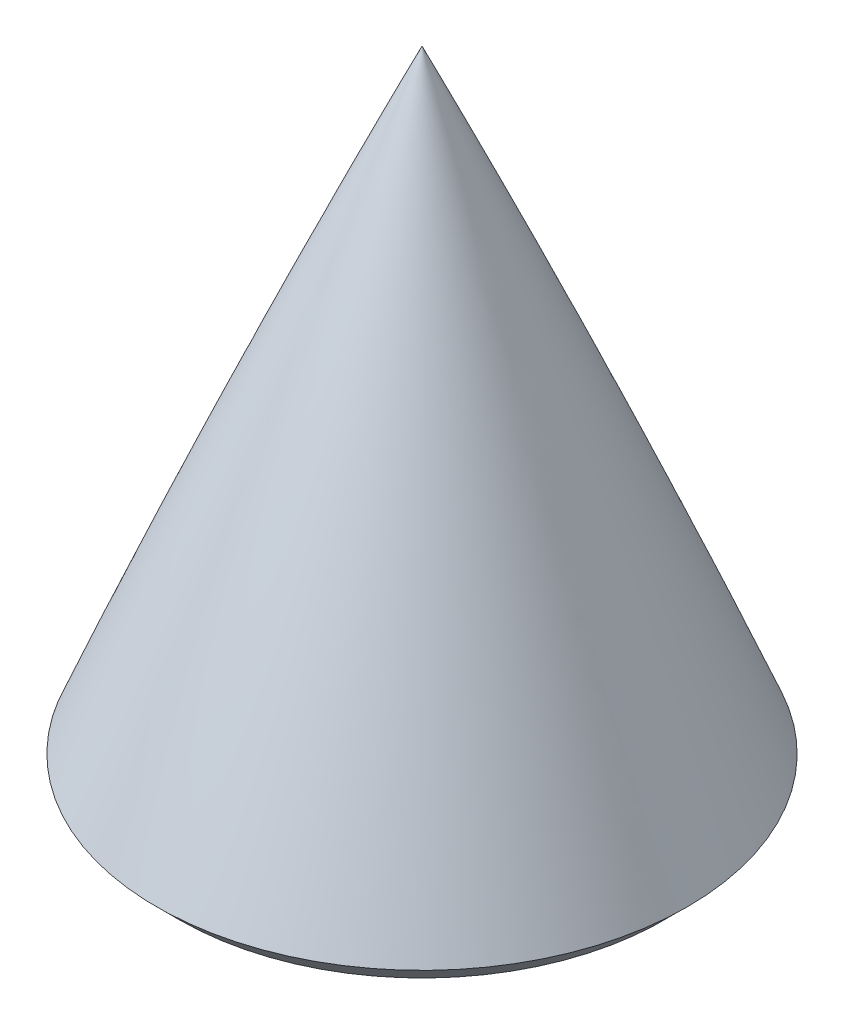
SolidWorks part; units mm, degrees
material "PVB"
ref_plane "Front Plane" through (0, 0, 0) normal (0, 0, 1) x (1, 0, 0)
ref_plane "Top Plane" through (0, 0, 0) normal (0, 1, 0) x (1, 0, 0)
ref_plane "Right Plane" through (0, 0, 0) normal (1, 0, 0) x (0, 0, -1)
sketch "Sketch2" plane through (0, 0, 0) normal (0, 0, 1) x (1, 0, 0)
  line L0 (0, 0) -> (0, 381) construction
  line L1 (-98.425, 0) -> (-90.551, 0)
  line L2 (0, 381) -> (0, 375.92)
  line L3 (0, 375.92) -> (0, 0)
  line L4 (0, 0) -> (-90.551, 0)
  arc A0 (0, 381) -> (-98.425, 0) centre (992.1135, -78.5092) ccw
  dimension "D1" = 381
  dimension "D2" = 5.08
  dimension "D3" = 98.425
  dimension "D4" = 7.874
revolve "Revolve1" add sketch "Sketch2" angle 360 about L2
sketch "Sketch3" plane through (0, 0, 0) normal (0, -1, 0) x (1, 0, 0)
  circle A0 centre (0, 0) radius 88.9
  circle A1 centre (0, 0) radius 86.995
  dimension "D1" = 177.8
extrude "Boss-Extrude1" [suppressed] add sketch "Sketch3" along normal blind 35.56
sketch "Sketch7" plane through (0, 0, 0) normal (0, -1, 0) x (1, 0, 0)
  circle A0 centre (-188.315, 83.0177) radius 421.4958
extrude "Cut-Extrude2" cut sketch "Sketch7" against normal blind 330.2
sketch "Sketch8" plane through (0, 330.2, 0) normal (0, -1, 0) x (-1, 0, 0)
  circle A0 centre (0, 0) radius 2.413
  dimension "D1" = 4.826
extrude "Cut-Extrude3" cut sketch "Sketch8" against normal blind 12.7
sketch "Sketch9" plane through (0, 0, 0) normal (0, 0, 1) x (1, 0, 0)
  line L0 (-20.066, 328.295) -> (-21.971, 330.2)
  line L1 (-21.971, 330.2) -> (-18.161, 330.2)
  line L2 (-18.161, 330.2) -> (-18.161, 328.295)
  line L3 (-18.161, 328.295) -> (-20.066, 328.295)
  line L4 (-21.9845, 330.2) -> (21.9845, 330.2) construction
  line L5 (0, 330.842) -> (0, 326.8398) construction
  dimension "D1" = 135
  dimension "D2" = 1.905
  dimension "D3" = 1.905
  dimension "D4" = 21.971
revolve "Revolve2" add sketch "Sketch9" angle 360 about L5
